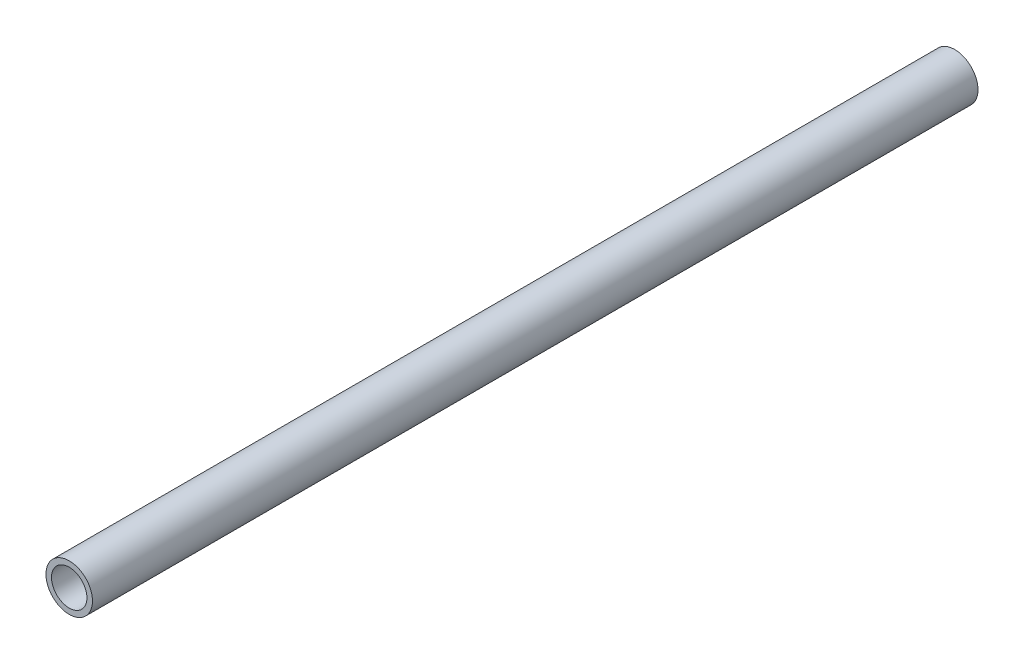
SolidWorks part; units mm, degrees
ref_plane "Front Plane" through (0, 0, 0) normal (0, 0, 1) x (1, 0, 0)
ref_plane "Top Plane" through (0, 0, 0) normal (0, 1, 0) x (1, 0, 0)
ref_plane "Right Plane" through (0, 0, 0) normal (1, 0, 0) x (0, 0, -1)
sketch "Sketch1" plane through (0, 0, 0) normal (0, 0, 1) x (1, 0, 0)
  circle A0 centre (0, 0) radius 5.25
  circle A1 centre (0, 0) radius 4
  dimension "D1" = 10.5
  dimension "D2" = 8
extrude "Boss-Extrude1" add sketch "Sketch1" against normal blind 200 contours A0 A1
